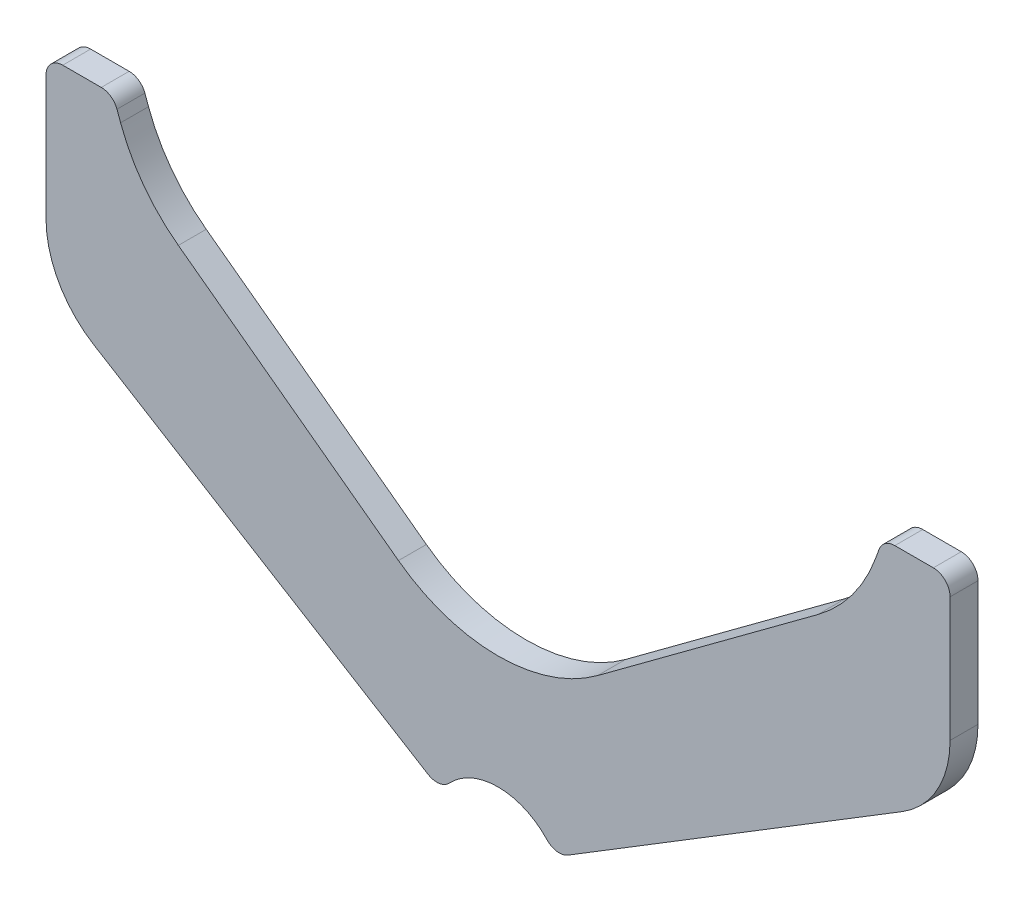
SolidWorks part; units mm, degrees
ref_plane "Plane1" through (0, 0, 0) normal (0, 0, 1) x (1, 0, 0)
ref_plane "Plane2" through (0, 0, 0) normal (0, 1, 0) x (1, 0, 0)
ref_plane "Plane3" through (0, 0, 0) normal (1, 0, 0) x (0, 0, -1)
sketch "Sketch1" plane through (0, 0, 0) normal (0, 0, 1) x (1, 0, 0)
  line L2 (-81, 82) -> (-81, 59.7173)
  line L3 (-72.405, 44.3698) -> (-12.5312, 7.6791)
  line L4 (0, 200) -> (0, 0) construction
  line L8 (-17.8447, 38.2044) -> (-57.2874, 67.3904)
  line L10 (-67.6335, 81.2455) -> (-68.2815, 83.0261)
  line L11 (-71.1006, 85) -> (-78, 85)
  line L13 (71.1006, 85) -> (78, 85)
  line L14 (67.6335, 81.2455) -> (68.2815, 83.0261)
  line L15 (17.8447, 38.2044) -> (57.2874, 67.3904)
  line L16 (72.405, 44.3698) -> (12.5312, 7.6791)
  line L17 (81, 82) -> (81, 59.7173)
  arc A0 (8.771, 8.1896) -> (-8.771, 8.1896) centre (0, 0) ccw
  arc A1 (12.5312, 7.6791) -> (8.771, 8.1896) centre (10.9637, 10.237) cw
  arc A2 (-12.5312, 7.6791) -> (-8.771, 8.1896) centre (-10.9637, 10.237) ccw
  arc A6 (-71.1006, 85) -> (-68.2815, 83.0261) centre (-71.1006, 82) cw
  arc A7 (-81, 82) -> (-78, 85) centre (-78, 82) cw
  arc A8 (68.2815, 83.0261) -> (71.1006, 85) centre (71.1006, 82) cw
  arc A9 (81, 82) -> (78, 85) centre (78, 82) ccw
  arc A10 (-72.405, 44.3698) -> (-81, 59.7173) centre (-63, 59.7173) cw
  arc A11 (81, 59.7173) -> (72.405, 44.3698) centre (63, 59.7173) cw
  arc A13 (57.2874, 67.3904) -> (67.6335, 81.2455) centre (39.4427, 91.5061) ccw
  arc A14 (-67.6335, 81.2455) -> (-57.2874, 67.3904) centre (-39.4427, 91.5061) ccw
  arc A15 (17.8447, 38.2044) -> (-17.8447, 38.2044) centre (0, 62.3201) cw
  point P3 (-69, 85)
  point P16 (-81, 85)
  point P34 (69, 85)
  point P37 (81, 85)
  point P40 (-81, 49.6369)
  point P43 (81, 49.6369)
  point P49 (64.5454, 72.7611)
  point P52 (-64.5454, 72.7611)
  point P55 (0, 25)
  dimension "D12" = 3
  dimension "D13" = 18
  dimension "D14" = 30
  dimension "D6" = 12
  dimension "D7" = 3
  dimension "D1" = 25
  dimension "D2" = 5
  dimension "D3" = 20
  dimension "D4" = 12
  dimension "D5" = 85
  dimension "D10" = 162
  dimension "D11" = 63
extrude "Base-Extrude" add sketch "Sketch1" along normal blind 5
